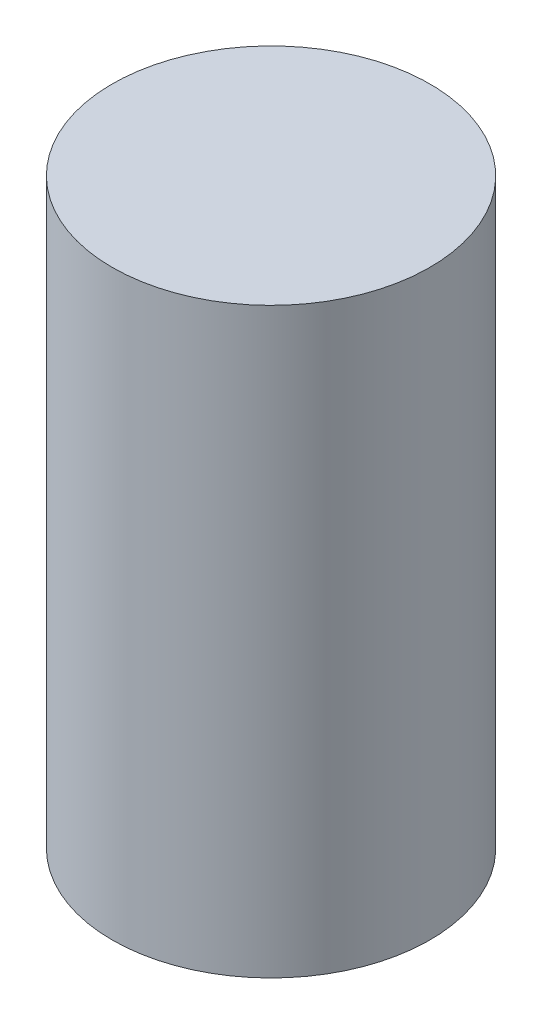
SolidWorks part; units mm, degrees
ref_plane "Front Plane" through (0, 0, 0) normal (0, 0, 1) x (1, 0, 0)
ref_plane "Top Plane" through (0, 0, 0) normal (0, 1, 0) x (1, 0, 0)
ref_plane "Right Plane" through (0, 0, 0) normal (1, 0, 0) x (0, 0, -1)
sketch "Sketch1" plane through (0, 0, 0) normal (0, 1, 0) x (1, 0, 0)
  circle A0 centre (0, 0) radius 3
  dimension "D1" = 6
extrude "Boss-Extrude1" add sketch "Sketch1" along normal blind 11
